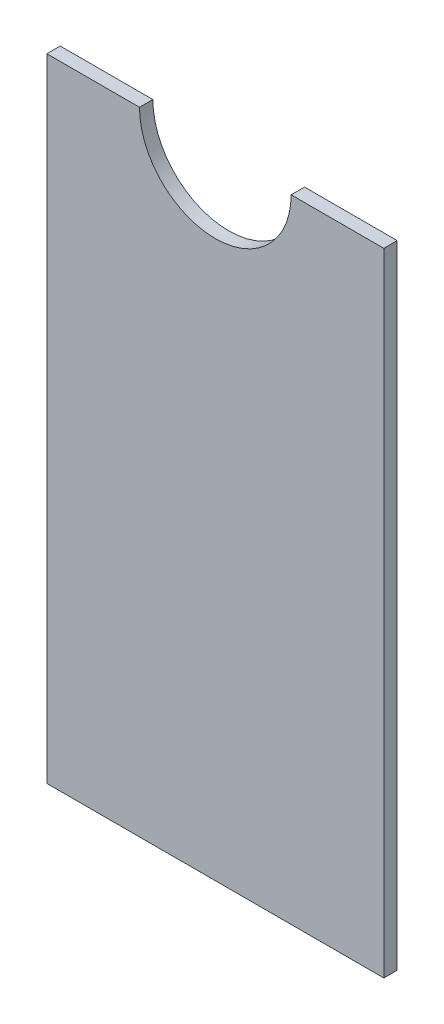
SolidWorks part; units mm, degrees
material "FiberBoard"
ref_plane "Front Plane" through (0, 0, 0) normal (0, 0, 1) x (1, 0, 0)
ref_plane "Top Plane" through (0, 0, 0) normal (0, 1, 0) x (1, 0, 0)
ref_plane "Right Plane" through (0, 0, 0) normal (1, 0, 0) x (0, 0, -1)
sketch "Sketch1" plane through (0, 0, 0) normal (0, 0, 1) x (1, 0, 0)
  line L0 (18, 75) -> (40, 75)
  line L1 (-40, 75) -> (-18, 75)
  line L2 (-40, 75) -> (-40, -75)
  line L3 (-40, -75) -> (40, -75)
  line L4 (40, 75) -> (40, -75)
  line L5 (-40, 75) -> (40, -75) construction
  line L6 (-40, -75) -> (40, 75) construction
  arc A0 (-18, 75) -> (18, 75) centre (0, 75) ccw
  point P0 (0, 0)
  point P7 (0, -75)
  dimension "D3" = 36
  dimension "D1" = 150
  dimension "D2" = 80
extrude "Boss-Extrude1" add sketch "Sketch1" along normal blind 3.175 contours L2 L3 L4 L0 A0 L1
